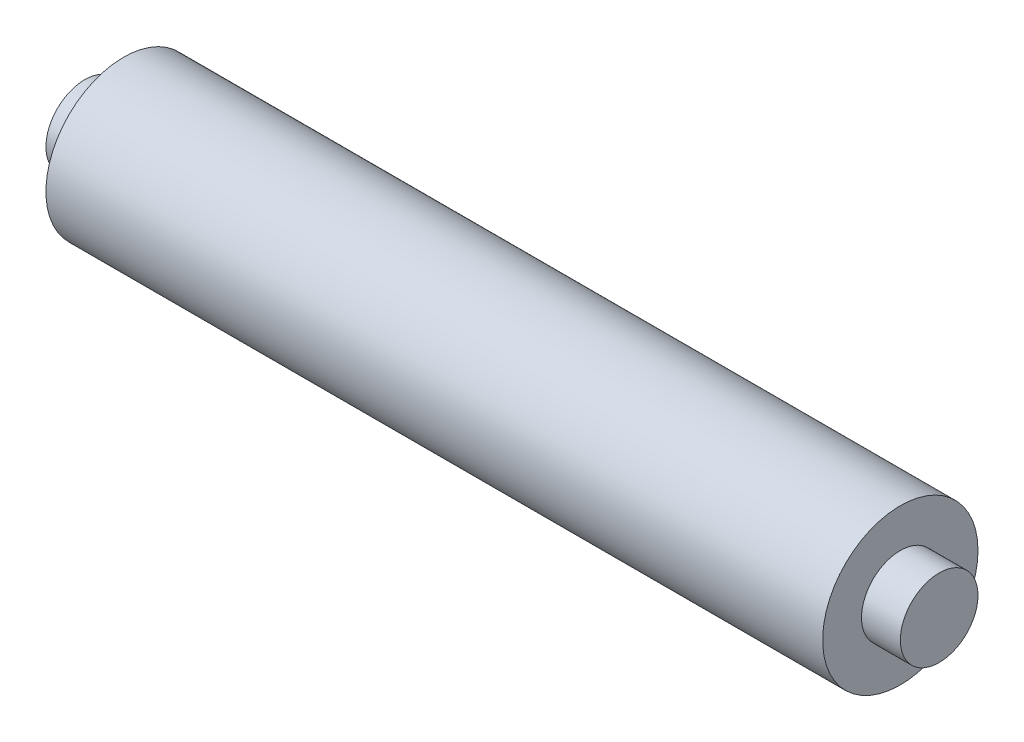
SolidWorks part; units mm, degrees
ref_plane "Front Plane" through (0, 0, 0) normal (0, 0, 1) x (1, 0, 0)
ref_plane "Top Plane" through (0, 0, 0) normal (0, 1, 0) x (1, 0, 0)
ref_plane "Right Plane" through (0, 0, 0) normal (1, 0, 0) x (0, 0, -1)
sketch "Sketch1" plane through (0, 0, 0) normal (1, 0, 0) x (0, 0, -1)
  circle A0 centre (0, 0) radius 76.2
  dimension "D1" = 152.4
extrude "Boss-Extrude1" add sketch "Sketch1" along normal blind 76.2
sketch "Sketch2" plane through (76.2, 0, 0) normal (1, 0, 0) x (0, 0, -1)
  circle A0 centre (0, 0) radius 152.4
  dimension "D1" = 304.8
extrude "Boss-Extrude2" add sketch "Sketch2" along normal blind 1524
sketch "Sketch3" plane through (1600.2, 0, 0) normal (1, 0, 0) x (0, 0, -1)
  circle A0 centre (0, 0) radius 76.2
  dimension "D1" = 152.4
extrude "Boss-Extrude3" add sketch "Sketch3" along normal blind 76.2
